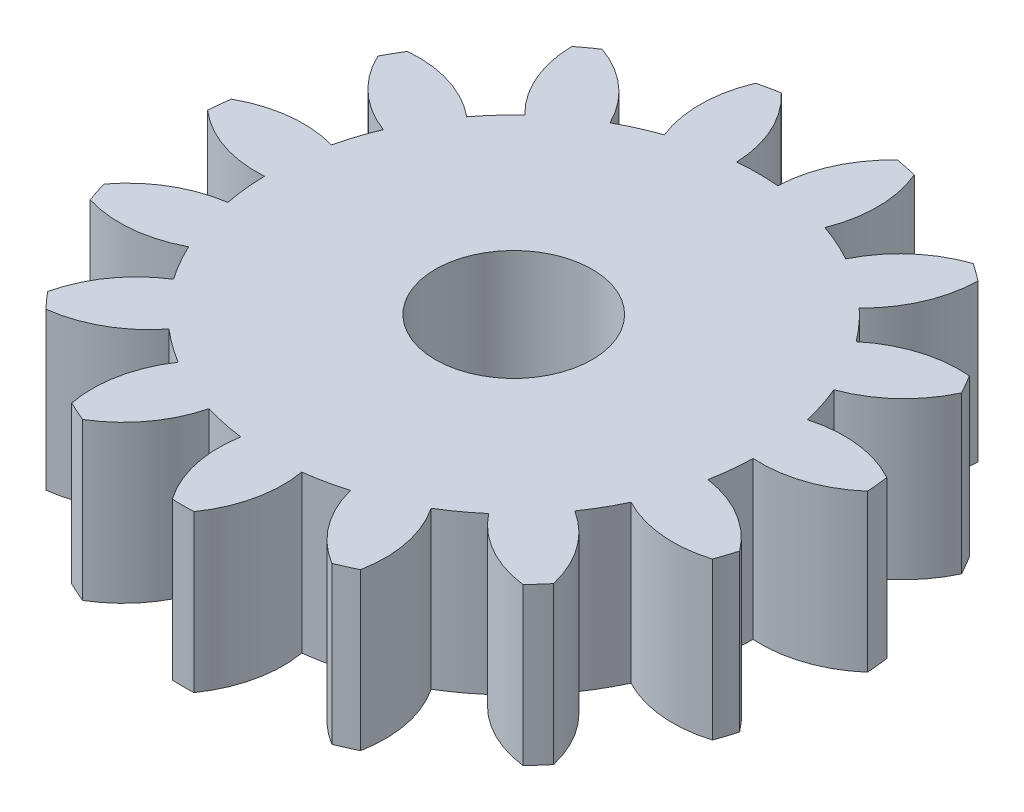
SolidWorks part; units mm, degrees
ref_plane "Front Plane" through (0, 0, 0) normal (0, 0, 1) x (1, 0, 0)
ref_plane "Top Plane" through (0, 0, 0) normal (0, 1, 0) x (1, 0, 0)
ref_plane "Right Plane" through (0, 0, 0) normal (1, 0, 0) x (0, 0, -1)
sketch "Sketch1" plane through (0, 0, 0) normal (0, 1, 0) x (1, 0, 0)
  circle A0 centre (0, 0) radius 1.5875
  arc A1 (-1.6254, 4.6755) -> (-2.387, 4.3365) centre (0, 0) ccw
  circle A2 centre (0, 0) radius 5.6 construction
  arc A3 (-3.7585, 5.5465) -> (-4.1136, 5.2885) centre (0, 0) ccw
  arc A4 (1.6254, 4.6755) -> (1.6069, 6.5045) centre (-0.6027, 5.5675) ccw
  arc A5 (-0.4168, 4.9324) -> (-1.1776, 6.5957) centre (-2.8151, 4.841) ccw
  arc A6 (1.1776, 6.5957) -> (0.4168, 4.9324) centre (2.8151, 4.841) ccw
  arc A7 (3.7585, 5.5465) -> (2.387, 4.3365) centre (4.5407, 3.2775) ccw
  arc A8 (3.3866, 3.6102) -> (4.1136, 5.2885) centre (1.7139, 5.3313) ccw
  arc A9 (5.6896, 3.5382) -> (3.9444, 2.9907) centre (5.4812, 1.1473) ccw
  arc A10 (4.5622, 1.9206) -> (5.909, 3.1582) centre (3.7342, 4.1732) ccw
  arc A11 (6.6368, 0.9182) -> (4.8198, 1.1278) centre (5.474, -1.1813) ccw
  arc A12 (4.949, -0.1011) -> (6.6827, 0.4818) centre (5.1088, 2.2936) ccw
  arc A13 (6.4365, -1.8606) -> (4.8618, -0.9301) centre (4.5202, -3.3057) ccw
  arc A14 (4.48, -2.1053) -> (6.3009, -2.278) centre (5.6, 0.0174) ccw
  arc A15 (5.1232, -4.3177) -> (4.0632, -2.8272) centre (2.7849, -4.8584) ccw
  arc A16 (3.2364, -3.7454) -> (4.8296, -4.6438) centre (5.1229, -2.2618) ccw
  arc A17 (2.9241, -6.0282) -> (2.562, -4.2354) centre (0.5681, -5.5711) ccw
  arc A18 (1.4332, -4.738) -> (2.5232, -6.2067) centre (3.76, -4.1499) ccw
  arc A19 (0.2194, -6.6964) -> (0.6178, -4.9113) centre (-1.747, -5.3205) ccw
  arc A20 (-0.6178, -4.9113) -> (-0.2194, -6.6964) centre (1.747, -5.3205) ccw
  arc A21 (-2.5232, -6.2067) -> (-1.4332, -4.738) centre (-3.76, -4.1499) ccw
  arc A22 (-2.562, -4.2354) -> (-2.9241, -6.0282) centre (-0.5681, -5.5711) ccw
  arc A23 (-4.8296, -4.6438) -> (-3.2364, -3.7454) centre (-5.1229, -2.2618) ccw
  arc A24 (-4.0632, -2.8272) -> (-5.1232, -4.3177) centre (-2.7849, -4.8584) ccw
  arc A25 (-6.3009, -2.278) -> (-4.48, -2.1053) centre (-5.6, 0.0174) ccw
  arc A26 (-4.8618, -0.9301) -> (-6.4365, -1.8606) centre (-4.5202, -3.3057) ccw
  arc A27 (-6.6827, 0.4818) -> (-4.949, -0.1011) centre (-5.1088, 2.2936) ccw
  arc A28 (-4.8198, 1.1278) -> (-6.6368, 0.9182) centre (-5.474, -1.1813) ccw
  arc A29 (-5.909, 3.1582) -> (-4.5622, 1.9206) centre (-3.7342, 4.1732) ccw
  arc A30 (-3.9444, 2.9907) -> (-5.6896, 3.5382) centre (-5.4812, 1.1473) ccw
  arc A31 (-3.3866, 3.6102) -> (-4.1136, 5.2885) centre (-1.7139, 5.3313) cw
  arc A32 (-2.387, 4.3365) -> (-3.7585, 5.5465) centre (-4.5407, 3.2775) ccw
  arc A33 (-1.6069, 6.5045) -> (-1.6254, 4.6755) centre (0.6027, 5.5675) ccw
  arc A34 (-1.1776, 6.5957) -> (-1.6069, 6.5045) centre (0, 0) ccw
  arc A35 (0.4168, 4.9324) -> (-0.4168, 4.9324) centre (0, 0) ccw
  arc A36 (2.387, 4.3365) -> (1.6254, 4.6755) centre (0, 0) ccw
  arc A37 (3.9444, 2.9907) -> (3.3866, 3.6102) centre (0, 0) ccw
  arc A38 (4.8198, 1.1278) -> (4.5622, 1.9206) centre (0, 0) ccw
  arc A39 (4.8618, -0.9301) -> (4.949, -0.1011) centre (0, 0) ccw
  arc A40 (4.0632, -2.8272) -> (4.48, -2.1053) centre (0, 0) ccw
  arc A41 (2.562, -4.2354) -> (3.2364, -3.7454) centre (0, 0) ccw
  arc A42 (0.6178, -4.9113) -> (1.4332, -4.738) centre (0, 0) ccw
  arc A43 (-1.4332, -4.738) -> (-0.6178, -4.9113) centre (0, 0) ccw
  arc A44 (-3.2364, -3.7454) -> (-2.562, -4.2354) centre (0, 0) ccw
  arc A45 (-4.48, -2.1053) -> (-4.0632, -2.8272) centre (0, 0) ccw
  arc A46 (-4.949, -0.1011) -> (-4.8618, -0.9301) centre (0, 0) ccw
  arc A47 (-4.5622, 1.9206) -> (-4.8198, 1.1278) centre (0, 0) ccw
  arc A48 (-3.3866, 3.6102) -> (-3.9444, 2.9907) centre (0, 0) ccw
  arc A49 (-5.6896, 3.5382) -> (-5.909, 3.1582) centre (0, 0) ccw
  arc A50 (-6.6368, 0.9182) -> (-6.6827, 0.4818) centre (0, 0) ccw
  arc A51 (-6.4365, -1.8606) -> (-6.3009, -2.278) centre (0, 0) ccw
  arc A52 (-5.1232, -4.3177) -> (-4.8296, -4.6438) centre (0, 0) ccw
  arc A53 (-2.9241, -6.0282) -> (-2.5232, -6.2067) centre (0, 0) ccw
  arc A54 (-0.2194, -6.6964) -> (0.2194, -6.6964) centre (0, 0) ccw
  arc A55 (2.5232, -6.2067) -> (2.9241, -6.0282) centre (0, 0) ccw
  arc A56 (4.8296, -4.6438) -> (5.1232, -4.3177) centre (0, 0) ccw
  arc A57 (6.3009, -2.278) -> (6.4365, -1.8606) centre (0, 0) ccw
  arc A58 (6.6827, 0.4818) -> (6.6368, 0.9182) centre (0, 0) ccw
  arc A59 (5.909, 3.1582) -> (5.6896, 3.5382) centre (0, 0) ccw
  arc A60 (4.1136, 5.2885) -> (3.7585, 5.5465) centre (0, 0) ccw
  arc A61 (1.6069, 6.5045) -> (1.1776, 6.5957) centre (0, 0) ccw
  point P14 (0.53, 5.5749)
  point P15 (-0.53, 5.5749)
  point P101 (0, 0)
  dimension "D1" = 6.7
  dimension "D2" = 5.6
  dimension "D3" = 4.95
  dimension "D4" = 3.175
  dimension "D5" = 2.4
  dimension "D6" = 15
  dimension "D7" = 1.06
  dimension "D8" = 0.53
extrude "Boss-Extrude1" add sketch "Sketch1" along normal blind 3.175
